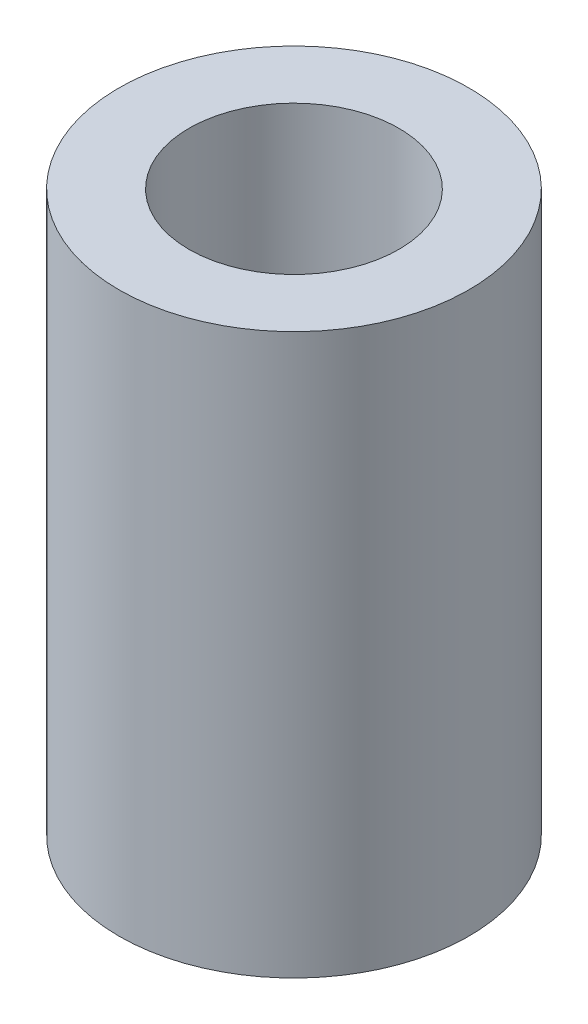
SolidWorks part; units mm, degrees
ref_plane "前视基准面" through (0, 0, 0) normal (0, 0, 1) x (1, 0, 0)
ref_plane "上视基准面" through (0, 0, 0) normal (0, 1, 0) x (1, 0, 0)
ref_plane "右视基准面" through (0, 0, 0) normal (1, 0, 0) x (0, 0, -1)
sketch "草图1" plane through (0, 0, 0) normal (0, 1, 0) x (1, 0, 0)
  circle A0 centre (0, 0) radius 1.5
  circle A1 centre (0, 0) radius 2.5
  dimension "D1" = 5
  dimension "D2" = 3
extrude "凸台-拉伸1" add sketch "草图1" along normal blind 8
